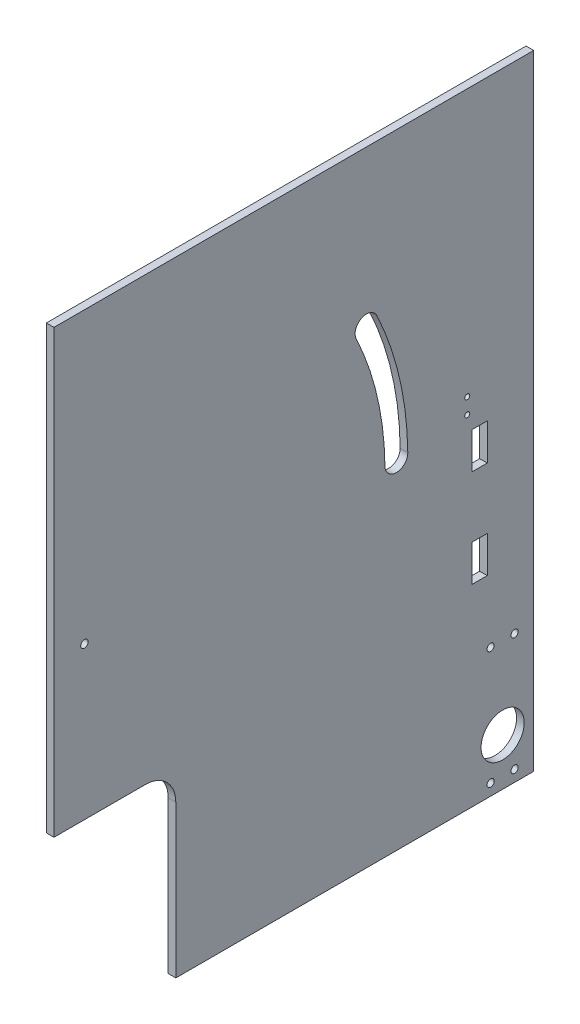
SolidWorks part; units mm, degrees
ref_plane "Front" through (0, 0, 0) normal (0, 0, 1) x (1, 0, 0)
ref_plane "Top" through (0, 0, 0) normal (0, 1, 0) x (1, 0, 0)
ref_plane "Right" through (0, 0, 0) normal (1, 0, 0) x (0, 0, -1)
sketch "Sketch1" plane through (0, 0, 0) normal (1, 0, 0) x (0, 0, -1)
  line L1 (-100.0125, 130.175) -> (100.0125, 130.175)
  line L2 (-100.0125, 130.175) -> (-100.0125, -130.175)
  line L3 (-100.0125, -130.175) -> (100.0125, -130.175)
  line L4 (100.0125, 130.175) -> (100.0125, -130.175)
  point P4 (-100.0125, 0)
  point P6 (0, 130.175)
  dimension "D1" = 260.35
  dimension "D2" = 200.025
extrude "Boss-Extrude1" add sketch "Sketch1" along normal blind 3.175
sketch "Sketch3" plane through (0, 0, 0) normal (-1, 0, 0) x (0, 0, 1)
  line L0 (-55.5625, 104.775) -> (77.7875, 104.775)
  line L1 (77.7875, 79.375) -> (-55.5625, 79.375)
  line L2 (-26.9875, 130.175) -> (-26.9875, -130.175) construction
  line L3 (-100.0125, 130.175) -> (100.0125, 130.175) construction
  line L4 (100.0125, -130.175) -> (-100.0125, -130.175) construction
  line L5 (100.0125, 130.175) -> (100.0125, -130.175) construction
  line L6 (-60.7375, 79.375) -> (-60.7375, 80.4772)
  line L12 (-55.5625, 92.075) -> (-68.2625, 92.075) construction
  arc A0 (77.7875, 104.775) -> (77.7875, 79.375) centre (77.7875, 92.075) cw
  arc A1 (-55.5625, 79.375) -> (-55.5625, 104.775) centre (-55.5625, 92.075) cw
  point P15 (90.4875, 92.075)
  dimension "D1" = 25.4
  dimension "D3" = 133.35
  dimension "D2" = 9.525
  dimension "D4" = 127
  dimension "D5" = 222.25
  dimension "D8" = 5.175
extrude "Cut-Extrude1" [suppressed] cut sketch "Sketch3" against normal through all contours A1 L1 A0 L0
sketch "Sketch6" plane through (3.175, 0, 0) normal (1, 0, 0) x (0, 0, -1)
  line L0 (117.5875, -88.265) -> (117.5875, -83.185)
  line L1 (139.5875, -83.185) -> (139.5875, -88.265)
  line L2 (111.5875, -103.765) -> (111.5875, -98.685)
  line L3 (114.5875, -103.765) -> (114.5875, -98.685)
  line L4 (111.5875, -72.765) -> (111.5875, -67.685)
  line L5 (114.5875, -72.765) -> (114.5875, -67.685)
  line L6 (128.5875, -83.185) -> (128.5875, -88.265) construction
  line L7 (145.5875, -103.765) -> (145.5875, -98.685)
  line L8 (142.5875, -103.765) -> (142.5875, -98.685)
  line L9 (142.5875, -72.765) -> (142.5875, -67.685)
  line L10 (145.5875, -72.765) -> (145.5875, -67.685)
  line L11 (-100.0125, 130.175) -> (-100.0125, -130.175) construction
  line L12 (-100.0125, -130.175) -> (100.0125, -130.175) construction
  arc A0 (117.5875, -88.265) -> (139.5875, -88.265) centre (128.5875, -88.265) ccw
  arc A1 (139.5875, -83.185) -> (117.5875, -83.185) centre (128.5875, -83.185) ccw
  arc A2 (111.5875, -103.765) -> (114.5875, -103.765) centre (113.0875, -103.765) ccw
  arc A3 (114.5875, -98.685) -> (111.5875, -98.685) centre (113.0875, -98.685) ccw
  arc A4 (111.5875, -72.765) -> (114.5875, -72.765) centre (113.0875, -72.765) ccw
  arc A5 (114.5875, -67.685) -> (111.5875, -67.685) centre (113.0875, -67.685) ccw
  arc A6 (145.5875, -103.765) -> (142.5875, -103.765) centre (144.0875, -103.765) cw
  arc A7 (142.5875, -98.685) -> (145.5875, -98.685) centre (144.0875, -98.685) cw
  arc A8 (145.5875, -72.765) -> (142.5875, -72.765) centre (144.0875, -72.765) cw
  arc A9 (142.5875, -67.685) -> (145.5875, -67.685) centre (144.0875, -67.685) cw
  circle A10 centre (113.0875, -69.36) radius 3.175
  circle A11 centre (144.0875, -69.36) radius 3.175
  circle A12 centre (113.0875, -102.09) radius 3.175
  circle A13 centre (144.0875, -102.09) radius 3.175
  point P37 (128.5875, -85.725)
  point P38 (139.5875, -85.725)
  dimension "D5" = 1.5
  dimension "D9" = 1.5
  dimension "D12" = 6.35
  dimension "D1" = 5.08
  dimension "D2" = 5.08
  dimension "D3" = 15.5
  dimension "D4" = 15.5
  dimension "D6" = 15.5
  dimension "D7" = 15.5
  dimension "D8" = 5.08
  dimension "D10" = 228.6
  dimension "D11" = 44.45
sketch "Sketch8" plane through (0, 0, 0) normal (-1, 0, 0) x (0, 0, 1)
  line L0 (100.0125, 130.175) -> (100.0125, -130.175) construction
  line L1 (100.0125, -130.175) -> (-100.0125, -130.175) construction
  line L3 (100.0125, -130.175) -> (-100.0125, -130.175) construction
  circle A0 centre (87.3125, 9.525) radius 1.55
  circle A5 centre (-72.3175, 18.925) radius 1.05
  circle A6 centre (-72.3175, 12.425) radius 1.05
  point P11 (-63.8175, 22.225)
  dimension "D1" = 3.1
  dimension "D15" = 3.3
  dimension "D8" = 2.1
  dimension "D2" = 12.7
  dimension "D3" = 139.7
  dimension "D6" = 151.13
  dimension "D7" = 152.4
  dimension "D9" = 6.5
  dimension "D12" = 8.5
extrude "Cut-Extrude7" cut sketch "Sketch8" against normal through all
sketch "Sketch9" plane through (0, 0, 0) normal (-1, 0, 0) x (0, 0, 1)
  line L0 (100.0125, 130.175) -> (100.0125, -130.175) construction
  line L1 (100.0125, -53.975) -> (49.2125, -53.975)
  line L2 (100.0125, -53.975) -> (100.0125, -130.175)
  line L3 (100.0125, -130.175) -> (49.2125, -130.175)
  line L4 (49.2125, -53.975) -> (49.2125, -130.175)
  line L5 (100.0125, -130.175) -> (-100.0125, -130.175) construction
  dimension "D1" = 50.8
  dimension "D2" = 76.2
extrude "Cut-Extrude8" cut sketch "Sketch9" against normal through all
fillet "Fillet1" radius 12.7 1 edges at (1.5875, -53.975, 49.2125)
sketch "Sketch10" plane through (0, 0, 0) normal (-1, 0, 0) x (0, 0, 1)
  line L4 (-42.8232, -130.175) -> (-42.8232, 6.325) construction
  line L5 (49.2125, -130.175) -> (-100.0125, -130.175) construction
  arc A9 (-28.2913, 69.3688) -> (-42.8232, 6.325) centre (87.3125, 9.525) ccw construction
  arc A10 (-34.6312, 67.0954) -> (-47.5281, 11.1443) centre (87.3125, 9.525) ccw
  arc A11 (-26.0179, 63.0289) -> (-38.0038, 11.03) centre (87.3125, 9.525) ccw
  arc A12 (-47.5281, 11.1443) -> (-38.0038, 11.03) centre (-42.766, 11.0872) ccw
  arc A13 (-34.6312, 67.0954) -> (-26.0179, 63.0289) centre (-30.3245, 65.0622) cw
  circle A14 centre (87.3125, 9.525) radius 125.3254 construction
  circle A15 centre (87.3125, 9.525) radius 130.175 construction
  circle A16 centre (87.3125, 9.525) radius 134.8504 construction
  point P23 (-28.2913, 69.3688)
  dimension "D1" = 4.7625
  dimension "D2" = 136.5
  dimension "D4" = 260.35
  dimension "D3" = 53.975
extrude "Cut-Extrude9" cut sketch "Sketch10" against normal through all
sketch "Sketch14" plane through (3.175, 0, 0) normal (1, 0, 0) x (0, 0, -1)
  line L0 (36.5125, -130.175) -> (36.5125, 130.175) construction
  line L5 (-49.2125, -130.175) -> (100.0125, -130.175) construction
  line L6 (100.0125, 130.175) -> (-100.0125, 130.175) construction
  line L7 (-100.0125, 130.175) -> (-100.0125, -53.975) construction
  line L14 (65.0875, -120.523) -> (65.0875, -126.873) construction
  circle A0 centre (-87.3125, 9.525) radius 181.0945 construction
  arc A1 (27.1013, -128.905) -> (33.4472, -122.7825) centre (27.1013, -122.555) ccw construction
  circle A2 centre (65.0875, -126.873) radius 1.5
  circle A3 centre (65.0875, -120.523) radius 1.5
  dimension "D6" = 3
  dimension "D7" = 6.35
  dimension "D1" = 136.525
  dimension "D8" = 3.302
  dimension "D9" = 28.575
extrude "Cut-Extrude11" [suppressed] cut sketch "Sketch14" against normal through all
sketch "Sketch15" plane through (3.175, 0, 0) normal (1, 0, 0) x (0, 0, -1)
  line L1 (74.3175, 6.075) -> (80.6675, 6.075)
  line L2 (74.3175, 6.075) -> (74.3175, -9.165)
  line L3 (74.3175, -9.165) -> (80.6675, -9.165)
  line L4 (80.6675, 6.075) -> (80.6675, -9.165)
  line L11 (74.3175, -34.565) -> (80.6675, -34.565)
  line L12 (74.3175, -34.565) -> (74.3175, -49.805)
  line L13 (74.3175, -49.805) -> (80.6675, -49.805)
  line L14 (80.6675, -34.565) -> (80.6675, -49.805)
  circle A0 centre (72.3175, 12.425) radius 1.05 construction
  dimension "D4" = 2
  dimension "D1" = 6.35
  dimension "D2" = 15.24
  dimension "D3" = 25.4
  dimension "D5" = 6.35
extrude "Cut-Extrude12" cut sketch "Sketch15" against normal through all
sketch "Sketch16" plane through (3.175, 0, 0) normal (1, 0, 0) x (0, 0, -1)
  line L0 (82.075, -76.4125) -> (92.075, -76.4125) construction
  line L1 (82.075, -76.4125) -> (82.075, -125.4125) construction
  line L2 (92.075, -76.4125) -> (92.075, -125.4125) construction
  line L3 (82.075, -125.4125) -> (92.075, -125.4125) construction
  line L4 (100.0125, -130.175) -> (100.0125, 130.175) construction
  line L6 (87.075, -125.4125) -> (87.075, -110.5625) construction
  line L7 (87.075, -119.5625) -> (68.66, -119.5625) construction
  line L9 (-49.2125, -130.175) -> (100.0125, -130.175) construction
  circle A0 centre (82.075, -125.4125) radius 1.5
  circle A1 centre (82.075, -76.4125) radius 1.5
  circle A2 centre (92.075, -125.4125) radius 1.5
  circle A3 centre (92.075, -76.4125) radius 1.5
  circle A4 centre (87.075, -110.5625) radius 9
  dimension "D1" = 3
  dimension "D7" = 18
  dimension "D2" = 10
  dimension "D3" = 49
  dimension "D4" = 14.85
  dimension "D5" = 7.9375
  dimension "D6" = 4.7625
extrude "Cut-Extrude13" cut sketch "Sketch16" against normal through all
equation "\"bottomThickness\"= .220in"
equation "\"wallThickness\"= .125in"
equation "\"D1@Boss-Extrude1\"=\"wallThickness\""
